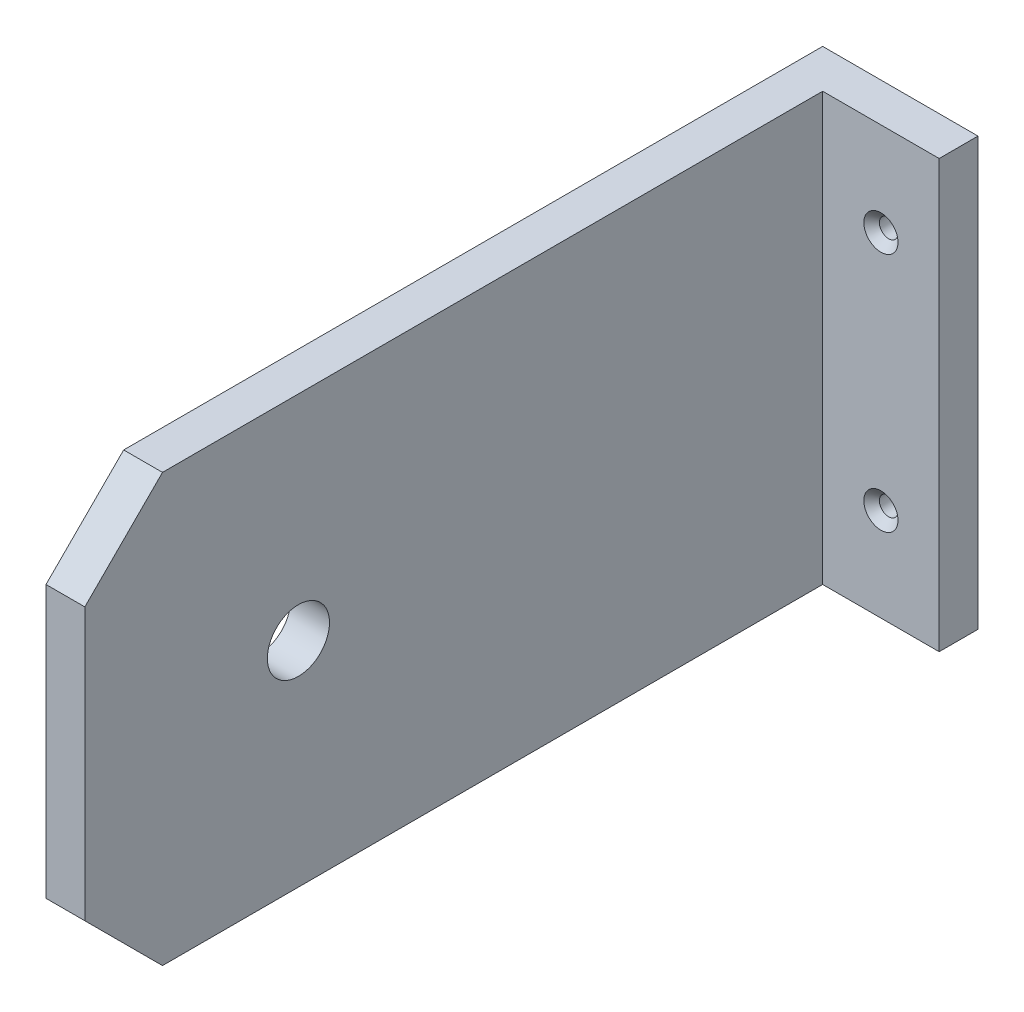
SolidWorks part; units mm, degrees
ref_plane "Ön Düzlem" through (0, 0, 0) normal (0, 0, 1) x (1, 0, 0)
ref_plane "Üst Düzlem" through (0, 0, 0) normal (0, 1, 0) x (1, 0, 0)
ref_plane "Sağ Düzlem" through (0, 0, 0) normal (1, 0, 0) x (0, 0, -1)
sketch "Sketch1" plane through (0, 0, 0) normal (1, 0, 0) x (0, 0, -1)
  line L1 (-50, 27.5) -> (50, 27.5)
  line L2 (-50, 27.5) -> (-50, -27.5)
  line L3 (-50, -27.5) -> (50, -27.5)
  line L4 (50, 27.5) -> (50, -27.5)
  line L5 (-50, 27.5) -> (50, -27.5) construction
  line L6 (-50, -27.5) -> (50, 27.5) construction
  point P0 (0, 0)
  dimension "D1" = 55
  dimension "D2" = 100
extrude "Boss-Extrude1" add sketch "Sketch1" along normal blind 5
sketch "Sketch2" plane through (5, 0, 0) normal (1, 0, 0) x (0, 0, -1)
  line L0 (-50, -27.5) -> (50, -27.5) construction
  line L1 (50, 27.5) -> (45, 27.5)
  line L2 (50, 27.5) -> (50, -27.5)
  line L3 (50, -27.5) -> (45, -27.5)
  line L4 (45, 27.5) -> (45, -27.5)
  dimension "D1" = 5
extrude "Boss-Extrude2" add sketch "Sketch2" along normal blind 15
sketch "Sketch3" plane through (0, 0, 0) normal (-1, 0, 0) x (0, 0, 1)
  line L0 (50, 27.5) -> (40, 27.5)
  line L1 (-50, 27.5) -> (50, 27.5) construction
  line L2 (40, 27.5) -> (50, 17.5)
  line L3 (50, 27.5) -> (50, -27.5) construction
  line L4 (50, 17.5) -> (50, 27.5)
  line L5 (50, -27.5) -> (40, -27.5)
  line L6 (50, -27.5) -> (-50, -27.5) construction
  line L7 (40, -27.5) -> (50, -17.5)
  line L8 (50, -17.5) -> (50, -27.5)
  dimension "D1" = 10
  dimension "D2" = 45
  dimension "D3" = 45
  dimension "D4" = 10
extrude "Cut-Extrude1" cut sketch "Sketch3" against normal up to next
hole_wizard "CSK for M2 Flat Head Machine Screw1" positions "Sketch5" profile "Sketch4" countersink size "M2" standard "ANSI Metric" end condition through all
sketch "Sketch5" plane through (0, 0, -45) normal (0, 0, 1) x (1, 0, 0)
  line L0 (20, 27.5) -> (5, 27.5) construction
  line L1 (20, -27.5) -> (5, -27.5) construction
  line L2 (5, 27.5) -> (5, -27.5) construction
  point P0 (12.5, 15.5)
  point P2 (12.5, -15.5)
  dimension "D1" = 12
  dimension "D2" = 12
  dimension "D3" = 7.5
  dimension "D4" = 7.5
sketch "Sketch4" plane through (12.5, 15.5, -45) normal (1, 0, 0) x (0, -1, 0)
  line L0 (0, 0) -> (0, 5)
  line L1 (0, 5) -> (1.2, 5)
  line L2 (1.2, 5) -> (1.2, 1)
  line L3 (1.2, 1) -> (2.2, 0)
  line L5 (2.2, 0) -> (0, 0)
  line L6 (-1.2, 1) -> (-2.2, 0) construction
  line L11 (0, -6.35) -> (0, 107.95) construction
  dimension "Thru Hole Dia." = 2.4
  dimension "Thru Hole Depth" = 5
  dimension "Near C'Sink Dia." = 4.4
  dimension "Near C'Sink Angle" = 90
sketch "Sketch6" plane through (0, 0, 0) normal (-1, 0, 0) x (0, 0, 1)
  circle A0 centre (22.5, 0) radius 4
  dimension "D1" = 8
extrude "Cut-Extrude2" cut sketch "Sketch6" against normal up to next
